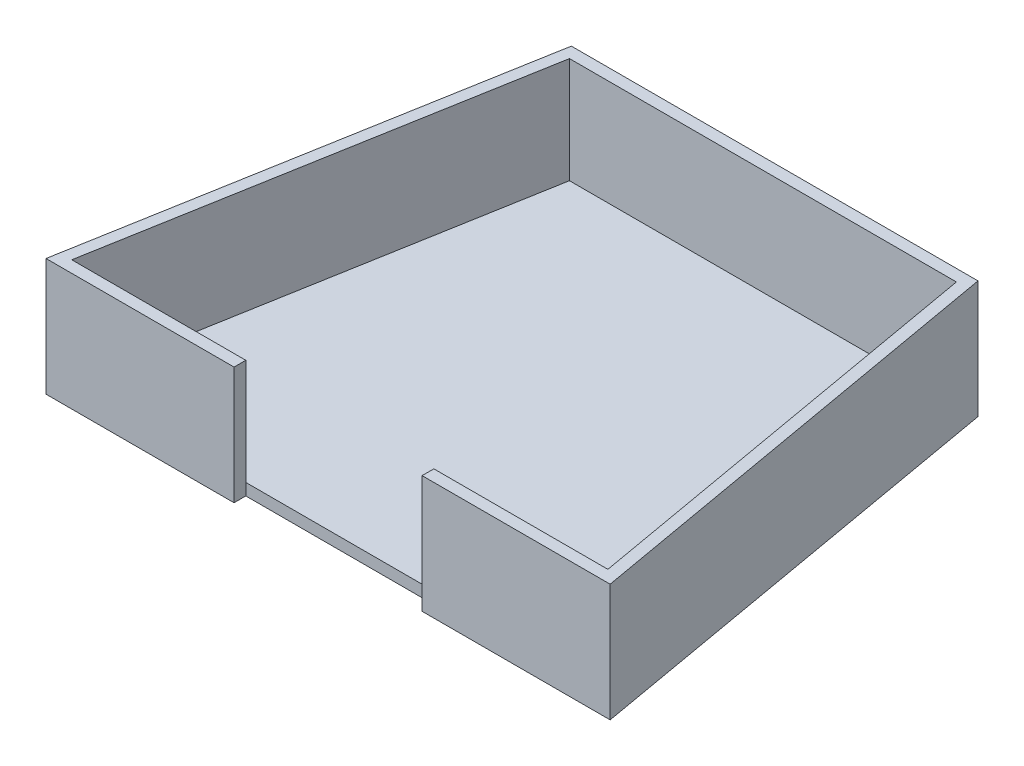
SolidWorks part; units mm, degrees
ref_plane "Front Plane" through (0, 0, 0) normal (0, 0, 1) x (1, 0, 0)
ref_plane "Top Plane" through (0, 0, 0) normal (0, 1, 0) x (1, 0, 0)
ref_plane "Right Plane" through (0, 0, 0) normal (1, 0, 0) x (0, 0, -1)
sketch "Sketch1" plane through (0, 0, 0) normal (0, 1, 0) x (1, 0, 0)
  line L0 (0, 0) -> (33.5021, 190)
  line L3 (240, 0) -> (0, 0)
  line L4 (33.5021, 190) -> (206.4979, 190)
  line L5 (206.4979, 190) -> (240, 0)
  dimension "D1" = 80
  dimension "D2" = 80
  dimension "D3" = 240
  dimension "D4" = 190
extrude "Boss-Extrude1" add sketch "Sketch1" along normal blind 50 separate body
shell "Shell2" thickness 5
sketch "Sketch3" plane through (0, 0, 0) normal (0, 0, 1) x (1, 0, 0)
  line L0 (120, 50) -> (120, 0) construction
  line L1 (0, 50) -> (240, 50) construction
  line L2 (0, 0) -> (240, 0) construction
  line L3 (80, 50) -> (80, 0)
  line L4 (160, 50) -> (160, 0)
  line L6 (80, 50) -> (160, 50)
  line L7 (80, 50) -> (80, 0)
  line L8 (80, 0) -> (160, 0)
  line L9 (160, 50) -> (160, 0)
  line M2 (0, 0) -> (240, 0)
  line M4 (240, 50) -> (0, 50)
  dimension "D1" = 40
  dimension "D2" = 40
extrude "Cut-Extrude1" cut sketch "Sketch3" against normal blind 5 contours L0 L6 L3 M2 | L0 L8 L4 M4
